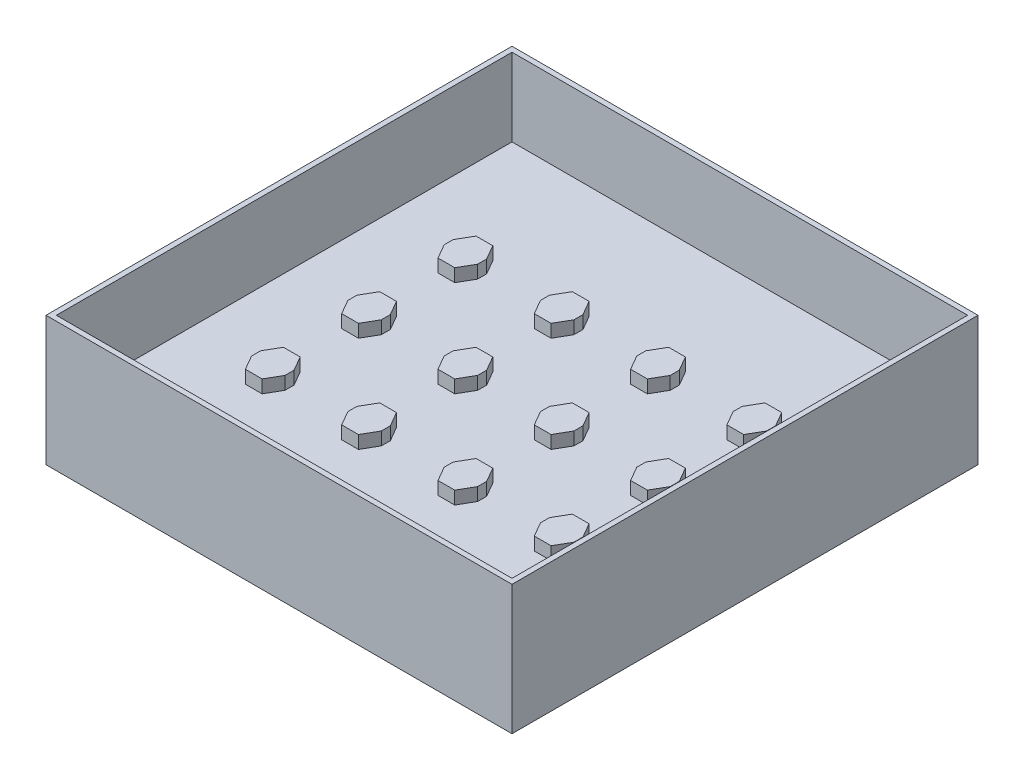
SolidWorks part; units mm, degrees
ref_plane "Front Plane" through (0, 0, 0) normal (0, 0, 1) x (1, 0, 0)
ref_plane "Top Plane" through (0, 0, 0) normal (0, 1, 0) x (1, 0, 0)
ref_plane "Right Plane" through (0, 0, 0) normal (1, 0, 0) x (0, 0, -1)
sketch "Sketch1" plane through (0, 0, 0) normal (0, 1, 0) x (1, 0, 0)
  line L1 (-45, -45) -> (45, -45)
  line L2 (-45, -45) -> (-45, 45)
  line L3 (-45, 45) -> (45, 45)
  line L4 (45, -45) -> (45, 45)
  line L5 (-45, -45) -> (45, 45) construction
  line L6 (-45, 45) -> (45, -45) construction
  point P0 (0, 0)
extrude "Boss-Extrude1" add sketch "Sketch1" along normal blind 3
sketch "Sketch3" plane through (0, 3, 0) normal (0, 1, 0) x (1, 0, 0)
  line L0 (0, 45) -> (0, -45) construction
  line L1 (45, 45) -> (-45, 45) construction
  line L2 (-45, -45) -> (45, -45) construction
  line L3 (-45, 0) -> (45, 0) construction
  line L4 (-45, 45) -> (-45, -45) construction
  line L5 (45, -45) -> (45, 45) construction
  circle A0 centre (0, 32.5) radius 1.5
  circle A1 centre (18.5, 32.4989) radius 1.5
  circle A2 centre (37, 32.4989) radius 1.5
  circle A3 centre (-37, 32.4989) radius 1.5
  circle A4 centre (-18.5, 32.4989) radius 1.5
  circle A5 centre (-18.5, -32.4989) radius 1.5
  circle A6 centre (-37, -32.4989) radius 1.5
  circle A7 centre (37, -32.4989) radius 1.5
  circle A8 centre (18.5, -32.4989) radius 1.5
  circle A9 centre (0, -32.5) radius 1.5
  dimension "D3" = 18.5
  dimension "D1" = 32.5
  dimension "D2" = 18.5
sketch "Sketch4" plane through (0, 3, 0) normal (0, 1, 0) x (1, 0, 0)
  line L0 (6.3668, 0.875) -> (6.3668, -0.875)
  line L100 (0, 45) -> (0, -45) construction
  line L101 (45, 45) -> (-45, 45) construction
  line L102 (-45, -45) -> (45, -45) construction
  line L103 (6.3668, 19.475) -> (6.3668, 17.725)
  line L104 (-45, 45) -> (-45, -45) construction
  line L105 (45, -45) -> (45, 45) construction
  line L106 (9.6, -45) -> (9.6, 45) construction
  line L107 (18.6, 45) -> (18.6, -45) construction
  line L108 (12.8332, 0.875) -> (11.2166, 3.675)
  line L109 (11.2166, 3.675) -> (7.9834, 3.675)
  line L110 (7.9834, 3.675) -> (6.3668, 0.875)
  line L114 (6.2518, 1.0742) -> (7.8684, -1.7258) [skipped]
  line L115 (7.0912, -1.925) -> (10.3243, -1.925) [skipped]
  line L116 (10.8855, -2.4985) -> (12.5021, 0.3015) [skipped]
  line L117 (12.8332, 0.875) -> (12.8332, 0)
  line L118 (6.3668, 0) -> (12.8332, 0) construction
  line L119 (12.8332, -0.875) -> (12.8332, 0)
  line L120 (12.8332, -0.875) -> (11.2166, -3.675)
  line L121 (11.2166, -3.675) -> (7.9834, -3.675)
  line L122 (7.9834, -3.675) -> (6.3668, -0.875)
  line L123 (-45, 0) -> (45, 0) construction
  line L124 (24.9668, 0.875) -> (24.9668, -0.875)
  line L125 (31.4332, 0.875) -> (29.8166, 3.675)
  line L126 (29.8166, 3.675) -> (26.5834, 3.675)
  line L127 (26.5834, 3.675) -> (24.9668, 0.875)
  line L128 (31.4332, 0.875) -> (31.4332, 0)
  line L129 (31.4332, -0.875) -> (31.4332, 0)
  line L130 (31.4332, -0.875) -> (29.8166, -3.675)
  line L131 (29.8166, -3.675) -> (26.5834, -3.675)
  line L132 (26.5834, -3.675) -> (24.9668, -0.875)
  line L133 (24.9668, 0) -> (31.4332, 0) construction
  line L134 (24.9668, -17.725) -> (24.9668, -19.475)
  line L135 (31.4332, -17.725) -> (29.8166, -14.925)
  line L136 (29.8166, -14.925) -> (26.5834, -14.925)
  line L137 (26.5834, -14.925) -> (24.9668, -17.725)
  line L138 (31.4332, -17.725) -> (31.4332, -18.6)
  line L139 (31.4332, -19.475) -> (31.4332, -18.6)
  line L140 (31.4332, -19.475) -> (29.8166, -22.275)
  line L141 (29.8166, -22.275) -> (26.5834, -22.275)
  line L142 (26.5834, -22.275) -> (24.9668, -19.475)
  line L143 (24.9668, -18.6) -> (31.4332, -18.6) construction
  line L144 (6.3668, -17.725) -> (6.3668, -19.475)
  line L145 (12.8332, -17.725) -> (11.2166, -14.925)
  line L146 (11.2166, -14.925) -> (7.9834, -14.925)
  line L147 (7.9834, -14.925) -> (6.3668, -17.725)
  line L148 (12.8332, -17.725) -> (12.8332, -18.6)
  line L149 (12.8332, -19.475) -> (12.8332, -18.6)
  line L150 (12.8332, -19.475) -> (11.2166, -22.275)
  line L151 (11.2166, -22.275) -> (7.9834, -22.275)
  line L152 (7.9834, -22.275) -> (6.3668, -19.475)
  line L153 (6.3668, -18.6) -> (12.8332, -18.6) construction
  line L154 (-30.8332, 0.875) -> (-30.8332, -0.875)
  line L155 (-24.3668, 0.875) -> (-25.9834, 3.675)
  line L156 (-25.9834, 3.675) -> (-29.2166, 3.675)
  line L157 (-29.2166, 3.675) -> (-30.8332, 0.875)
  line L158 (-24.3668, 0.875) -> (-24.3668, 0)
  line L159 (-24.3668, -0.875) -> (-24.3668, 0)
  line L160 (-24.3668, -0.875) -> (-25.9834, -3.675)
  line L161 (-25.9834, -3.675) -> (-29.2166, -3.675)
  line L162 (-29.2166, -3.675) -> (-30.8332, -0.875)
  line L163 (-12.2332, 0.875) -> (-12.2332, -0.875)
  line L164 (-5.7668, 0.875) -> (-7.3834, 3.675)
  line L165 (-7.3834, 3.675) -> (-10.6166, 3.675)
  line L166 (-10.6166, 3.675) -> (-12.2332, 0.875)
  line L167 (-5.7668, 0.875) -> (-5.7668, 0)
  line L168 (-5.7668, -0.875) -> (-5.7668, 0)
  line L169 (-5.7668, -0.875) -> (-7.3834, -3.675)
  line L170 (-7.3834, -3.675) -> (-10.6166, -3.675)
  line L171 (-10.6166, -3.675) -> (-12.2332, -0.875)
  line L172 (-12.2332, -17.725) -> (-12.2332, -19.475)
  line L173 (-5.7668, -17.725) -> (-7.3834, -14.925)
  line L174 (-7.3834, -14.925) -> (-10.6166, -14.925)
  line L175 (-10.6166, -14.925) -> (-12.2332, -17.725)
  line L176 (-5.7668, -17.725) -> (-5.7668, -18.6)
  line L177 (-5.7668, -19.475) -> (-5.7668, -18.6)
  line L178 (-5.7668, -19.475) -> (-7.3834, -22.275)
  line L179 (-7.3834, -22.275) -> (-10.6166, -22.275)
  line L180 (-10.6166, -22.275) -> (-12.2332, -19.475)
  line L181 (-30.8332, -17.725) -> (-30.8332, -19.475)
  line L182 (-24.3668, -17.725) -> (-25.9834, -14.925)
  line L183 (-25.9834, -14.925) -> (-29.2166, -14.925)
  line L184 (-29.2166, -14.925) -> (-30.8332, -17.725)
  line L185 (-24.3668, -17.725) -> (-24.3668, -18.6)
  line L186 (-24.3668, -19.475) -> (-24.3668, -18.6)
  line L187 (-24.3668, -19.475) -> (-25.9834, -22.275)
  line L188 (-25.9834, -22.275) -> (-29.2166, -22.275)
  line L189 (-29.2166, -22.275) -> (-30.8332, -19.475)
  line L190 (-30.8332, 0) -> (-24.3668, 0) construction
  line L191 (-12.2332, 0) -> (-5.7668, 0) construction
  line L192 (-12.2332, -18.6) -> (-5.7668, -18.6) construction
  line L193 (-30.8332, -18.6) -> (-24.3668, -18.6) construction
  line L194 (12.8332, 19.475) -> (11.2166, 22.275)
  line L195 (11.2166, 22.275) -> (7.9834, 22.275)
  line L196 (7.9834, 22.275) -> (6.3668, 19.475)
  line L197 (12.8332, 19.475) -> (12.8332, 18.6)
  line L198 (12.8332, 17.725) -> (12.8332, 18.6)
  line L199 (12.8332, 17.725) -> (11.2166, 14.925)
  line L200 (11.2166, 14.925) -> (7.9834, 14.925)
  line L201 (7.9834, 14.925) -> (6.3668, 17.725)
  line L202 (24.9668, 19.475) -> (24.9668, 17.725)
  line L203 (31.4332, 19.475) -> (29.8166, 22.275)
  line L204 (29.8166, 22.275) -> (26.5834, 22.275)
  line L205 (26.5834, 22.275) -> (24.9668, 19.475)
  line L206 (31.4332, 19.475) -> (31.4332, 18.6)
  line L207 (31.4332, 17.725) -> (31.4332, 18.6)
  line L208 (31.4332, 17.725) -> (29.8166, 14.925)
  line L209 (29.8166, 14.925) -> (26.5834, 14.925)
  line L210 (26.5834, 14.925) -> (24.9668, 17.725)
  line L211 (-30.8332, 19.475) -> (-30.8332, 17.725)
  line L212 (-24.3668, 19.475) -> (-25.9834, 22.275)
  line L213 (-25.9834, 22.275) -> (-29.2166, 22.275)
  line L214 (-29.2166, 22.275) -> (-30.8332, 19.475)
  line L215 (-24.3668, 19.475) -> (-24.3668, 18.6)
  line L216 (-24.3668, 17.725) -> (-24.3668, 18.6)
  line L217 (-24.3668, 17.725) -> (-25.9834, 14.925)
  line L218 (-25.9834, 14.925) -> (-29.2166, 14.925)
  line L219 (-29.2166, 14.925) -> (-30.8332, 17.725)
  line L220 (-12.2332, 19.475) -> (-12.2332, 17.725)
  line L221 (-5.7668, 19.475) -> (-7.3834, 22.275)
  line L222 (-7.3834, 22.275) -> (-10.6166, 22.275)
  line L223 (-10.6166, 22.275) -> (-12.2332, 19.475)
  line L224 (-5.7668, 19.475) -> (-5.7668, 18.6)
  line L225 (-5.7668, 17.725) -> (-5.7668, 18.6)
  line L226 (-5.7668, 17.725) -> (-7.3834, 14.925)
  line L227 (-7.3834, 14.925) -> (-10.6166, 14.925)
  line L228 (-10.6166, 14.925) -> (-12.2332, 17.725)
  line L229 (6.3668, 18.6) -> (12.8332, 18.6) construction
  line L230 (24.9668, 18.6) -> (31.4332, 18.6) construction
  line L231 (-30.8332, 18.6) -> (-24.3668, 18.6) construction
  line L232 (-12.2332, 18.6) -> (-5.7668, 18.6) construction
  point P6 (9.6, 0)
  point P16 (9.6, 0)
  point P24 (-27.6, 0)
  point P35 (9.6, 18.6)
  point P41 (28.2, 0)
  point P52 (28.2, -18.6)
  point P63 (9.6, -18.6)
  point P83 (-9, 0)
  point P94 (-9, -18.6)
  point P105 (-27.6, -18.6)
  point P116 (9.6, 18.6)
  point P123 (-27.6, 18.6)
  point P129 (28.2, 18.6)
  point P149 (-9, 18.6)
  dimension "D1" = 9
  dimension "D2" = 18.6
  dimension "D5" = 1.75
  dimension "D3" = 3.2332
  dimension "D4" = 3.2332
  dimension "D7" = 1.75
  dimension "D6" = 3.2332
  dimension "D8" = 2
  dimension "D9" = 2
extrude "Boss-Extrude2" [suppressed] add sketch "Sketch3" along normal blind 15
extrude "Boss-Extrude3" add sketch "Sketch4" along normal blind 2.5
sketch "Sketch6" plane through (0, 3, 0) normal (0, 1, 0) x (1, 0, 0)
  line L1 (-44, 44) -> (44, 44)
  line L2 (-44, 44) -> (-44, -44)
  line L3 (-44, -44) -> (44, -44)
  line L4 (44, 44) -> (44, -44)
  line L5 (-44, 44) -> (44, -44) construction
  line L6 (-44, -44) -> (44, 44) construction
  line L7 (-45, 45) -> (45, 45)
  line L8 (-45, 45) -> (-45, -45)
  line L9 (-45, -45) -> (45, -45)
  line L10 (45, 45) -> (45, -45)
  line L11 (-45, 45) -> (45, -45) construction
  line L12 (-45, -45) -> (45, 45) construction
  point P0 (0, 0)
  point P6 (0, 0)
  dimension "D1" = 88
  dimension "D2" = 88
extrude "Boss-Extrude4" add sketch "Sketch6" along normal blind 15 and the other way blind 10
